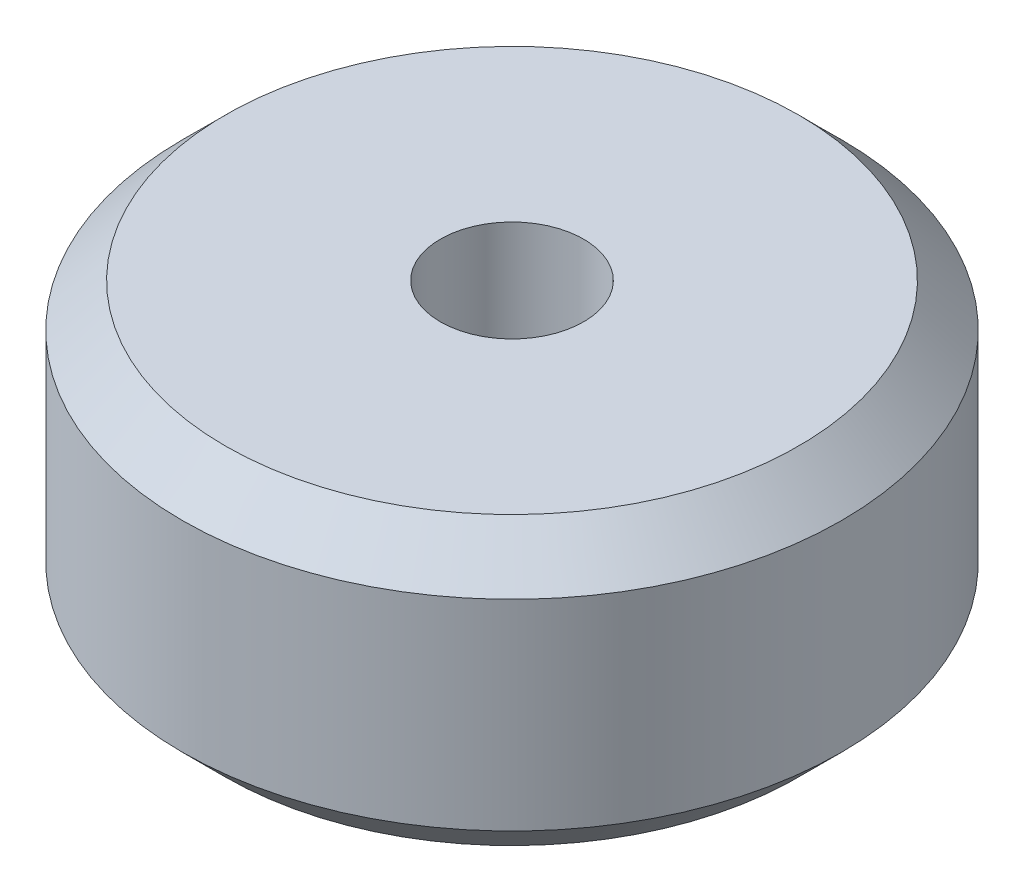
SolidWorks part; units mm, degrees
ref_plane "Front" through (0, 0, 0) normal (0, 0, 1) x (1, 0, 0)
ref_plane "Top" through (0, 0, 0) normal (0, 1, 0) x (1, 0, 0)
ref_plane "Right" through (0, 0, 0) normal (1, 0, 0) x (0, 0, -1)
sketch "Sketch1" plane through (0, 0, 0) normal (0, 0, 1) x (1, 0, 0)
  line L0 (2.5, 5) -> (10, 5)
  line L1 (10, 5) -> (11.5, 3.5)
  line L2 (11.5, 3.5) -> (11.5, -3.5)
  line L3 (11.5, -3.5) -> (10, -5)
  line L4 (10, -5) -> (2.5, -5)
  line L5 (2.5, -5) -> (2.5, 5)
  point P2 (2.5, 0)
  point P7 (11.5, 0)
  point P9 (0, 0)
  point P10 (8.3333, -5)
  dimension "D1" = 2.5
  dimension "D2" = 11.5
  dimension "D3" = 10
  dimension "D4" = 10
ref_axis "Axis1" through (0, 50, 0) along (0, -1, 0)
revolve "Revolve1" add sketch "Sketch1" angle 360 about axis through (0, 50, 0) along (0, -1, 0)
